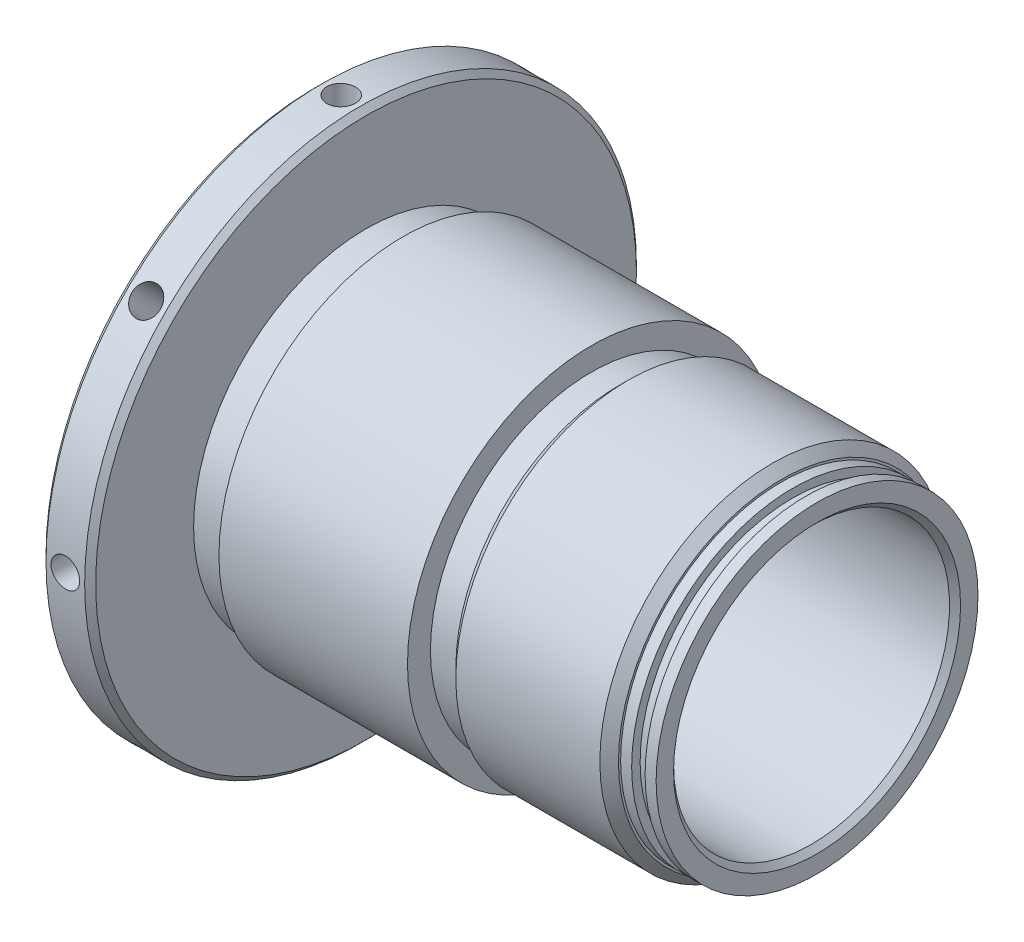
SolidWorks part; units mm, degrees
material "AISI 440C PER AMS 5630"
ref_plane "XY" through (0, 0, 0) normal (0, 0, 1) x (1, 0, 0)
ref_plane "XZ" through (0, 0, 0) normal (0, 1, 0) x (1, 0, 0)
ref_plane "YZ" through (0, 0, 0) normal (1, 0, 0) x (0, 0, -1)
sketch "Sketch1" plane through (0, 0, 0) normal (0, 0, 1) x (1, 0, 0)
  line L0 (0, 0) -> (105.4936, 0) construction
  line L1 (0, 19.3548) -> (0, 25.3937)
  line L3 (19.304, 20.1168) -> (19.304, 27.5145) construction
  line L4 (0, 25.3937) -> (62.2808, 25.3937)
  line L5 (17.78, 20.1168) -> (20.828, 20.1168)
  line L6 (62.2808, 19.0563) -> (21.8884, 19.0563)
  line L8 (17.018, 19.3548) -> (0, 19.3548)
  line L9 (17.78, 20.1168) -> (17.018, 19.3548)
  line L10 (20.828, 20.1168) -> (21.8884, 19.0563)
  line L12 (62.2808, 25.3937) -> (62.2808, 19.0563)
  point P8 (25.908, 19.0563)
  point P18 (12.7, 19.3548)
  dimension "D2" = 19.304
  dimension "D8" = 0.762
  dimension "D12" = 135
  dimension "D5" = 38.1127
  dimension "D3" = 38.7096
  dimension "D4" = 3.048
  dimension "D6" = 62.2808
  dimension "D7" = 50.7873
  dimension "D11" = 13.208
  dimension "D13" = 135
revolve "Revolve1" add sketch "Sketch1" angle 360 about L0
sketch "Sketch2" plane through (0, 0, 0) normal (0, 0, 1) x (1, 0, 0)
  line L0 (62.2808, 25.3937) -> (0, 25.3937) construction
  line L1 (31.115, 25.3937) -> (62.2808, 25.3937)
  line L2 (31.115, 25.3937) -> (31.115, 22.225)
  line L3 (34.925, 23.8125) -> (57.3786, 23.8125)
  line L4 (62.2808, 25.3937) -> (62.2808, 22.225)
  line L5 (62.2808, -25.3937) -> (62.2808, 25.3937) construction
  line L6 (0, 0) -> (36.2503, 0) construction
  line L7 (2.8458, 22.5298) -> (34.9432, 22.5298) construction
  line L8 (34.925, 22.225) -> (34.925, 23.8125)
  line L9 (31.115, 22.225) -> (34.925, 22.225)
  line L10 (60.7568, 22.225) -> (62.2808, 22.225)
  line L12 (58.9026, 22.225) -> (58.9026, 21.0566)
  line L13 (58.9026, 21.0566) -> (60.7568, 21.0566)
  line L14 (60.7568, 22.225) -> (60.7568, 21.0566)
  line L16 (57.3786, 23.8125) -> (57.3786, 22.225)
  line L17 (57.3786, 22.225) -> (58.9026, 22.225)
  dimension "D3" = 44.45
  dimension "D1" = 5.207
  dimension "D2" = 47.625
  dimension "D4" = 45.0596
  dimension "D5" = 3.81
  dimension "D6" = 42.1132
  dimension "D7" = 1.524
  dimension "D8" = 1.8542
  dimension "D9" = 1.524
revolve "Cut-Revolve1" cut sketch "Sketch2" angle 360 about L6
cosmetic thread "Cosmetic Thread1" parameters "D2"=45.0596
ref_plane "Plane1" through (25.908, 0, 0) normal (1, 0, 0) x (0, 0, -1)
chamfer "Chamfer1" distance 0.762 angle 45 1 edges at (62.2808, 0, 19.0563)
sketch "Sketch3" plane through (0, 0, 0) normal (0, 0, 1) x (1, 0, 0)
  line L0 (0, 0) -> (-41.4207, 0) construction
  line L1 (17.018, 19.3548) -> (0, 19.3548) construction
  line L2 (0, 19.3548) -> (-6.858, 19.3548)
  line L3 (0, 19.3548) -> (0, 38.1)
  line L4 (0, 38.1) -> (-6.858, 38.1)
  line L5 (-6.858, 19.3548) -> (-6.858, 38.1)
  line L6 (0, 25.3937) -> (0, -25.3937) construction
  dimension "D1" = 6.858
  dimension "D2" = 76.2
revolve "Revolve2" add sketch "Sketch3" angle 360 about L0
sketch "Sketch5" plane through (0, 0, 0) normal (0, 0, 1) x (1, 0, 0)
  line L0 (31.115, 25.3937) -> (0, 25.3937) construction
  line L1 (5.08, 25.3937) -> (0, 25.3937)
  line L2 (5.08, 25.3937) -> (5.08, 23.8125)
  line L3 (5.08, 23.8125) -> (0, 23.8125)
  line L4 (0, 25.3937) -> (0, 23.8125)
  line L5 (0, -38.1) -> (0, 38.1) construction
  line L6 (23.3533, 0) -> (53.789, 0) construction
  line L7 (0, 0) -> (105.4936, 0) construction
  dimension "D1" = 5.08
  dimension "D2" = 47.625
revolve "Cut-Revolve2" cut sketch "Sketch5" angle 360 about L6
chamfer "Chamfer3" distance 0.762 angle 45 2 edges at (0, 0, -38.1) (-6.858, 0, -38.1)
ref_plane "Plane2" through (-3.429, 38.1, 0) normal (0, 1, 0) x (0, 0, 1)
sketch "Sketch6" plane through (-3.429, 38.1, 0) normal (0, 1, 0) x (0, 0, 1)
  line L0 (0, 0) -> (12.4962, 0) construction
  line L1 (37.338, 3.429) -> (-37.338, 3.429) construction
  line L2 (-19.3548, -3.429) -> (19.3548, -3.429) construction
  line L3 (0, 3.429) -> (0, 108.9226) construction
  circle A0 centre (0, 0) radius 1.9812
  dimension "D1" = 3.9624
extrude "Cut-Extrude2" cut sketch "Sketch6" against normal blind 6.35
pattern_circular "CirPattern1" count 8 over 360 about axis through (0, 0, 0) along (1, 0, 0) of "Cut-Extrude2"
chamfer "Chamfer4" distance 1.2827 angle 45 2 edges at (34.925, 0, 23.8125) (57.3786, 0, 23.8125)
sketch "Sketch7" plane through (-6.858, 0, 0) normal (-1, 0, 0) x (0, 0, 1)
  line L0 (-13.1177, 25.1162) -> (13.1177, 25.1162) construction
  line L1 (0, 25.1162) -> (0, 0) construction
  text T0 "STG 1-2"
extrude "Extrude1" cut sketch "Sketch7" against normal blind 0.0254
